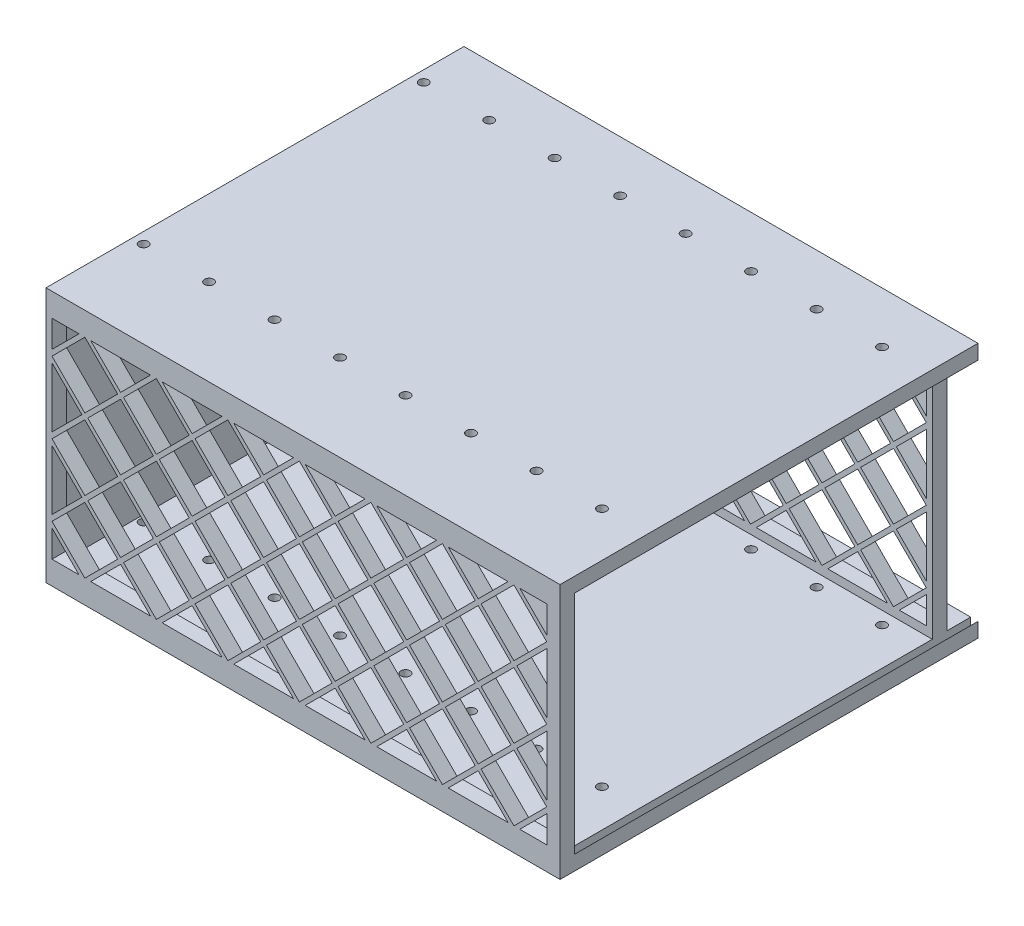
SolidWorks part; units mm, degrees
ref_plane "Front Plane" through (0, 0, 0) normal (0, 0, 1) x (1, 0, 0)
ref_plane "Top Plane" through (0, 0, 0) normal (0, 1, 0) x (1, 0, 0)
ref_plane "Right Plane" through (0, 0, 0) normal (1, 0, 0) x (0, 0, -1)
sketch "Sketch1" plane through (0, 0, 0) normal (0, 1, 0) x (1, 0, 0)
  line L1 (0, 0) -> (140.589, 0)
  line L2 (0, 0) -> (0, 114.3)
  line L3 (0, 114.3) -> (140.589, 114.3)
  line L4 (140.589, 0) -> (140.589, 114.3)
  dimension "D1" = 140.589
  dimension "D2" = 114.3
extrude "Boss-Extrude1" add sketch "Sketch1" along normal blind 69.85
sketch "Sketch4" plane through (140.589, 0, 0) normal (1, 0, 0) x (0, 0, -1)
  line L0 (114.3, 69.85) -> (114.3, 0) construction
  line L1 (114.3, 65.85) -> (107.8, 65.85)
  line L2 (114.3, 65.85) -> (114.3, 4)
  line L3 (114.3, 4) -> (107.8, 4)
  line L4 (107.8, 65.85) -> (107.8, 4)
  line L5 (107.8, 0) -> (107.8, 4) construction
  line L6 (0, 0) -> (114.3, 0) construction
  line L7 (107.8, 65.85) -> (107.8, 69.85) construction
  line L8 (0, 69.85) -> (114.3, 69.85) construction
  dimension "D1" = 6.5
  dimension "D2" = 4
extrude "Cut-Extrude2" cut sketch "Sketch4" against normal through all
sketch "Sketch3" plane through (140.589, 0, 0) normal (1, 0, 0) x (0, 0, -1)
  line L0 (4, 65.85) -> (0, 65.85) construction
  line L1 (4, 65.85) -> (103.8, 65.85)
  line L2 (4, 65.85) -> (4, 4)
  line L3 (4, 4) -> (103.8, 4)
  line L4 (103.8, 65.85) -> (103.8, 4)
  line L5 (0, 69.85) -> (0, 0) construction
  line L6 (103.8, 4) -> (107.8, 4) construction
  line L8 (103.8, 0) -> (103.8, 4) construction
  line L9 (0, 0) -> (114.3, 0) construction
  line L10 (4, 65.85) -> (4, 69.85) construction
  line L11 (0, 69.85) -> (114.3, 69.85) construction
  line L12 (107.8, 65.85) -> (107.8, 4) construction
  dimension "D1" = 4
extrude "Cut-Extrude3" cut sketch "Sketch3" against normal offset from surface (139.389 mm away) 1.2 up to face at (0, 34.925, -84.1)
sketch "Sketch2" plane through (0, 69.85, 0) normal (0, 1, 0) x (1, 0, 0)
  line L0 (0, 23.7) -> (140.589, 23.7) construction
  line L1 (0, 114.3) -> (0, 0) construction
  line L2 (140.589, 0) -> (140.589, 114.3) construction
  line L3 (0, 100.3) -> (140.589, 100.3) construction
  line L4 (25.527, 100.3) -> (25.527, 23.7) construction
  line L5 (140.589, 114.3) -> (0, 114.3) construction
  line L6 (43.434, 100.3) -> (43.434, 23.7) construction
  line L7 (61.341, 100.3) -> (61.341, 23.7) construction
  line L8 (79.248, 100.3) -> (79.248, 23.7) construction
  line L9 (97.155, 100.3) -> (97.155, 23.7) construction
  line L10 (115.062, 100.3) -> (115.062, 23.7) construction
  line L11 (132.969, 100.3) -> (132.969, 23.7) construction
  line L12 (7.62, 100.3) -> (7.62, 23.7) construction
  line L13 (7.62, 62) -> (25.527, 62) construction
  line L14 (25.527, 62) -> (43.434, 62) construction
  line L15 (43.434, 62) -> (61.341, 62) construction
  line L16 (61.341, 62) -> (79.248, 62) construction
  line L17 (79.248, 62) -> (97.155, 62) construction
  line L18 (97.155, 62) -> (115.062, 62) construction
  line L19 (115.062, 62) -> (132.969, 62) construction
  line L20 (7.62, 62) -> (0, 62) construction
  line L21 (132.969, 62) -> (140.589, 62) construction
  line L22 (3, 100.3) -> (3, 23.7) construction
  circle A0 centre (3, 100.3) radius 1.25
  circle A1 centre (3, 23.7) radius 1.25
  circle A2 centre (20.907, 100.3) radius 1.25
  circle A3 centre (20.907, 23.7) radius 1.25
  circle A4 centre (38.814, 100.3) radius 1.25
  circle A5 centre (38.814, 23.7) radius 1.25
  circle A6 centre (56.721, 100.3) radius 1.25
  circle A7 centre (56.721, 23.7) radius 1.25
  circle A8 centre (74.628, 100.3) radius 1.25
  circle A9 centre (74.628, 23.7) radius 1.25
  circle A10 centre (92.535, 100.3) radius 1.25
  circle A11 centre (92.535, 23.7) radius 1.25
  circle A12 centre (110.442, 100.3) radius 1.25
  circle A13 centre (110.442, 23.7) radius 1.25
  circle A14 centre (128.349, 100.3) radius 1.25
  circle A15 centre (128.349, 23.7) radius 1.25
  dimension "D4" = 3
  dimension "D5" = 2.5
  dimension "D1" = 14
  dimension "D2" = 90.6
  dimension "D3" = 17.907
  dimension "D7" = 17.907
  dimension "D6" = 8
extrude "Cut-Extrude1" cut sketch "Sketch2" against normal blind 4
ref_plane "Plane1" through (0, 34.925, 0) normal (0, 1, 0) x (1, 0, 0)
mirror "Mirror1" about plane through (0, 34.925, 0) normal (0, 1, 0) of "Cut-Extrude1"
sketch "Sketch5" plane through (0, 0, -114.3) normal (0, 0, -1) x (-1, 0, 0)
  line L0 (-138.589, 67.85) -> (-138.589, 2)
  line L1 (-138.589, 2) -> (-140.589, 4)
  line L2 (0, 4) -> (-140.589, 4) construction
  line L3 (-140.589, 4) -> (-140.589, 65.85)
  line L4 (0, 65.85) -> (-140.589, 65.85) construction
  line L5 (-140.589, 65.85) -> (-138.589, 67.85)
  line L6 (-138.589, 67.85) -> (-138.589, 69.85) construction
  line L7 (-140.589, 69.85) -> (0, 69.85) construction
  line L8 (-138.589, 2) -> (-138.589, 0) construction
  line L9 (-140.589, 0) -> (0, 0) construction
  line L10 (-140.589, 69.85) -> (-140.589, 65.85) construction
  dimension "D1" = 2
  dimension "D2" = 2
extrude "Cut-Extrude4" cut sketch "Sketch5" against normal up to surface (110.3 mm away) up to face at (70.8945, 34.925, -4)
sketch "Sketch6" plane through (0, 0, -107.8) normal (0, 0, -1) x (-1, 0, 0)
  line L0 (-136.9488, 54.483) -> (-127.9685, 45.5027)
  line L1 (-127.9685, 45.5027) -> (-118.9882, 54.483)
  line L2 (-118.9882, 54.483) -> (-127.9685, 63.4633)
  line L3 (-127.9685, 63.4633) -> (-136.9488, 54.483)
  line L4 (-108.4105, 63.4633) -> (-117.3908, 54.483)
  line L5 (-117.3908, 54.483) -> (-108.4105, 45.5027)
  line L6 (-108.4105, 45.5027) -> (-99.4302, 54.483)
  line L7 (-99.4302, 54.483) -> (-108.4105, 63.4633)
  line L8 (-88.8525, 63.4633) -> (-97.8328, 54.483)
  line L9 (-97.8328, 54.483) -> (-88.8525, 45.5027)
  line L10 (-88.8525, 45.5027) -> (-79.8722, 54.483)
  line L11 (-79.8722, 54.483) -> (-88.8525, 63.4633)
  line L12 (-69.2945, 63.4633) -> (-78.2748, 54.483)
  line L13 (-78.2748, 54.483) -> (-69.2945, 45.5027)
  line L14 (-69.2945, 45.5027) -> (-60.3142, 54.483)
  line L15 (-60.3142, 54.483) -> (-69.2945, 63.4633)
  line L16 (-49.7365, 63.4633) -> (-58.7168, 54.483)
  line L17 (-58.7168, 54.483) -> (-49.7365, 45.5027)
  line L18 (-49.7365, 45.5027) -> (-40.7562, 54.483)
  line L19 (-40.7562, 54.483) -> (-49.7365, 63.4633)
  line L20 (-30.1785, 63.4633) -> (-39.1588, 54.483)
  line L21 (-39.1588, 54.483) -> (-30.1785, 45.5027)
  line L22 (-30.1785, 45.5027) -> (-21.1982, 54.483)
  line L23 (-21.1982, 54.483) -> (-30.1785, 63.4633)
  line L24 (-10.6205, 63.4633) -> (-19.6008, 54.483)
  line L25 (-19.6008, 54.483) -> (-10.6205, 45.5027)
  line L26 (-10.6205, 45.5027) -> (-1.6402, 54.483)
  line L27 (-1.6402, 54.483) -> (-10.6205, 63.4633)
  line L28 (-108.4105, 43.9053) -> (-117.3908, 34.925)
  line L29 (-117.3908, 34.925) -> (-108.4105, 25.9447)
  line L30 (-108.4105, 25.9447) -> (-99.4302, 34.925)
  line L31 (-99.4302, 34.925) -> (-108.4105, 43.9053)
  line L32 (-88.8525, 43.9053) -> (-97.8328, 34.925)
  line L33 (-97.8328, 34.925) -> (-88.8525, 25.9447)
  line L34 (-88.8525, 25.9447) -> (-79.8722, 34.925)
  line L35 (-79.8722, 34.925) -> (-88.8525, 43.9053)
  line L36 (-69.2945, 43.9053) -> (-78.2748, 34.925)
  line L37 (-78.2748, 34.925) -> (-69.2945, 25.9447)
  line L38 (-69.2945, 25.9447) -> (-60.3142, 34.925)
  line L39 (-60.3142, 34.925) -> (-69.2945, 43.9053)
  line L40 (-49.7365, 43.9053) -> (-58.7168, 34.925)
  line L41 (-58.7168, 34.925) -> (-49.7365, 25.9447)
  line L42 (-49.7365, 25.9447) -> (-40.7562, 34.925)
  line L43 (-40.7562, 34.925) -> (-49.7365, 43.9053)
  line L44 (-30.1785, 43.9053) -> (-39.1588, 34.925)
  line L45 (-39.1588, 34.925) -> (-30.1785, 25.9447)
  line L46 (-30.1785, 25.9447) -> (-21.1982, 34.925)
  line L47 (-21.1982, 34.925) -> (-30.1785, 43.9053)
  line L48 (-10.6205, 43.9053) -> (-19.6008, 34.925)
  line L49 (-19.6008, 34.925) -> (-10.6205, 25.9447)
  line L50 (-10.6205, 25.9447) -> (-1.6402, 34.925)
  line L51 (-1.6402, 34.925) -> (-10.6205, 43.9053)
  line L52 (-108.4105, 24.3473) -> (-117.3908, 15.367)
  line L53 (-117.3908, 15.367) -> (-108.4105, 6.3867)
  line L54 (-108.4105, 6.3867) -> (-99.4302, 15.367)
  line L55 (-99.4302, 15.367) -> (-108.4105, 24.3473)
  line L56 (-88.8525, 24.3473) -> (-97.8328, 15.367)
  line L57 (-97.8328, 15.367) -> (-88.8525, 6.3867)
  line L58 (-88.8525, 6.3867) -> (-79.8722, 15.367)
  line L59 (-79.8722, 15.367) -> (-88.8525, 24.3473)
  line L60 (-69.2945, 24.3473) -> (-78.2748, 15.367)
  line L61 (-78.2748, 15.367) -> (-69.2945, 6.3867)
  line L62 (-69.2945, 6.3867) -> (-60.3142, 15.367)
  line L63 (-60.3142, 15.367) -> (-69.2945, 24.3473)
  line L64 (-49.7365, 24.3473) -> (-58.7168, 15.367)
  line L65 (-58.7168, 15.367) -> (-49.7365, 6.3867)
  line L66 (-49.7365, 6.3867) -> (-40.7562, 15.367)
  line L67 (-40.7562, 15.367) -> (-49.7365, 24.3473)
  line L68 (-30.1785, 24.3473) -> (-39.1588, 15.367)
  line L69 (-39.1588, 15.367) -> (-30.1785, 6.3867)
  line L70 (-30.1785, 6.3867) -> (-21.1982, 15.367)
  line L71 (-21.1982, 15.367) -> (-30.1785, 24.3473)
  line L72 (-10.6205, 24.3473) -> (-19.6008, 15.367)
  line L73 (-19.6008, 15.367) -> (-10.6205, 6.3867)
  line L74 (-10.6205, 6.3867) -> (-1.6402, 15.367)
  line L75 (-1.6402, 15.367) -> (-10.6205, 24.3473)
  line L76 (-127.9685, 43.9053) -> (-136.9488, 34.925)
  line L77 (-136.9488, 34.925) -> (-127.9685, 25.9447)
  line L78 (-127.9685, 25.9447) -> (-118.9882, 34.925)
  line L79 (-118.9882, 34.925) -> (-127.9685, 43.9053)
  line L80 (-127.9685, 24.3473) -> (-136.9488, 15.367)
  line L81 (-136.9488, 15.367) -> (-127.9685, 6.3867)
  line L82 (-127.9685, 6.3867) -> (-118.9882, 15.367)
  line L83 (-118.9882, 15.367) -> (-127.9685, 24.3473)
  line L84 (-127.9685, 63.4633) -> (-108.4105, 63.4633) construction
  line L85 (-127.9685, 63.4633) -> (-127.9685, 43.9053) construction
  line L86 (-136.9488, 54.483) -> (-138.589, 54.483) construction
  line L87 (-138.589, 65.85) -> (-138.589, 4) construction
  line L88 (0, 54.483) -> (-1.6402, 54.483) construction
  line L89 (0, 65.85) -> (0, 4) construction
  line L90 (-127.9685, 4) -> (-127.9685, 6.3867) construction
  line L91 (0, 4) -> (-138.589, 4) construction
  line L92 (-127.9685, 6.3867) -> (-127.9685, 65.85) construction
  line L93 (0, 65.85) -> (-138.589, 65.85) construction
  line L94 (-127.9685, 65.85) -> (-127.9685, 63.4633) construction
  line L95 (-127.1698, 44.704) -> (-118.1895, 35.7237)
  line L96 (-118.1895, 35.7237) -> (-109.2092, 44.704)
  line L97 (-109.2092, 44.704) -> (-118.1895, 53.6843)
  line L98 (-118.1895, 53.6843) -> (-127.1698, 44.704)
  line L99 (-122.6796, 49.1941) -> (-123.4784, 49.9929) construction
  line L100 (-113.6994, 49.1941) -> (-112.9006, 49.9929) construction
  line L101 (-107.6118, 44.704) -> (-98.6315, 35.7237)
  line L102 (-98.6315, 35.7237) -> (-89.6512, 44.704)
  line L103 (-89.6512, 44.704) -> (-98.6315, 53.6843)
  line L104 (-98.6315, 53.6843) -> (-107.6118, 44.704)
  line L105 (-88.0538, 44.704) -> (-79.0735, 35.7237)
  line L106 (-79.0735, 35.7237) -> (-70.0932, 44.704)
  line L107 (-70.0932, 44.704) -> (-79.0735, 53.6843)
  line L108 (-79.0735, 53.6843) -> (-88.0538, 44.704)
  line L109 (-68.4958, 44.704) -> (-59.5155, 35.7237)
  line L110 (-59.5155, 35.7237) -> (-50.5352, 44.704)
  line L111 (-50.5352, 44.704) -> (-59.5155, 53.6843)
  line L112 (-59.5155, 53.6843) -> (-68.4958, 44.704)
  line L113 (-48.9378, 44.704) -> (-39.9575, 35.7237)
  line L114 (-39.9575, 35.7237) -> (-30.9772, 44.704)
  line L115 (-30.9772, 44.704) -> (-39.9575, 53.6843)
  line L116 (-39.9575, 53.6843) -> (-48.9378, 44.704)
  line L117 (-29.3798, 44.704) -> (-20.3995, 35.7237)
  line L118 (-20.3995, 35.7237) -> (-11.4192, 44.704)
  line L119 (-11.4192, 44.704) -> (-20.3995, 53.6843)
  line L120 (-20.3995, 53.6843) -> (-29.3798, 44.704)
  line L121 (-107.6118, 25.146) -> (-98.6315, 16.1657)
  line L122 (-98.6315, 16.1657) -> (-89.6512, 25.146)
  line L123 (-89.6512, 25.146) -> (-98.6315, 34.1263)
  line L124 (-98.6315, 34.1263) -> (-107.6118, 25.146)
  line L125 (-88.0538, 25.146) -> (-79.0735, 16.1657)
  line L126 (-79.0735, 16.1657) -> (-70.0932, 25.146)
  line L127 (-70.0932, 25.146) -> (-79.0735, 34.1263)
  line L128 (-79.0735, 34.1263) -> (-88.0538, 25.146)
  line L129 (-68.4958, 25.146) -> (-59.5155, 16.1657)
  line L130 (-59.5155, 16.1657) -> (-50.5352, 25.146)
  line L131 (-50.5352, 25.146) -> (-59.5155, 34.1263)
  line L132 (-59.5155, 34.1263) -> (-68.4958, 25.146)
  line L133 (-48.9378, 25.146) -> (-39.9575, 16.1657)
  line L134 (-39.9575, 16.1657) -> (-30.9772, 25.146)
  line L135 (-30.9772, 25.146) -> (-39.9575, 34.1263)
  line L136 (-39.9575, 34.1263) -> (-48.9378, 25.146)
  line L137 (-29.3798, 25.146) -> (-20.3995, 16.1657)
  line L138 (-20.3995, 16.1657) -> (-11.4192, 25.146)
  line L139 (-11.4192, 25.146) -> (-20.3995, 34.1263)
  line L140 (-20.3995, 34.1263) -> (-29.3798, 25.146)
  line L141 (-127.1698, 25.146) -> (-118.1895, 16.1657)
  line L142 (-118.1895, 16.1657) -> (-109.2092, 25.146)
  line L143 (-109.2092, 25.146) -> (-118.1895, 34.1263)
  line L144 (-118.1895, 34.1263) -> (-127.1698, 25.146)
  line L145 (-127.1698, 44.704) -> (-107.6118, 44.704) construction
  line L146 (-127.1698, 44.704) -> (-127.1698, 25.146) construction
  line L147 (-136.9488, 52.8855) -> (-136.9488, 36.5225)
  line L148 (-136.9488, 36.5225) -> (-128.7672, 44.704)
  line L149 (-128.7672, 44.704) -> (-136.9488, 52.8855)
  line L150 (-128.7672, 44.704) -> (-127.9685, 45.5027) construction
  line L151 (-128.7672, 44.704) -> (-127.9685, 43.9053) construction
  line L152 (-128.7672, 25.146) -> (-136.9488, 33.3275)
  line L153 (-136.9488, 33.3275) -> (-136.9488, 16.9645)
  line L154 (-136.9488, 16.9645) -> (-128.7672, 25.146)
  line L155 (-128.7672, 44.704) -> (-128.7672, 25.146) construction
  line L156 (-69.2945, 65.85) -> (-69.2945, 4) construction
  line L157 (-136.9488, 56.0805) -> (-136.9488, 63.4633)
  line L158 (-136.9488, 63.4633) -> (-129.566, 63.4633)
  line L159 (-129.566, 63.4633) -> (-136.9488, 56.0805)
  line L160 (-132.4586, 58.9731) -> (-133.2574, 59.7719) construction
  line L161 (-127.9685, 63.4633) -> (-129.566, 63.4633) construction
  line L162 (-136.9488, 13.7695) -> (-136.9488, 6.3867)
  line L163 (-136.9488, 6.3867) -> (-129.566, 6.3867)
  line L164 (-129.566, 6.3867) -> (-136.9488, 13.7695)
  line L165 (-132.4586, 10.8769) -> (-133.2574, 10.0781) construction
  line L166 (-136.9488, 13.7695) -> (-136.9488, 15.367) construction
  line L167 (-129.566, 6.3867) -> (-127.9685, 6.3867) construction
  line L168 (-1.6402, 6.3867) -> (-9.023, 6.3867)
  line L169 (-1.6402, 13.7695) -> (-1.6402, 6.3867)
  line L170 (-9.023, 6.3867) -> (-1.6402, 13.7695)
  line L171 (-1.6402, 16.9645) -> (-9.8218, 25.146)
  line L172 (-1.6402, 33.3275) -> (-1.6402, 16.9645)
  line L173 (-9.8218, 25.146) -> (-1.6402, 33.3275)
  line L174 (-1.6402, 36.5225) -> (-9.8218, 44.704)
  line L175 (-1.6402, 52.8855) -> (-1.6402, 36.5225)
  line L176 (-9.8218, 44.704) -> (-1.6402, 52.8855)
  line L177 (-1.6402, 63.4633) -> (-9.023, 63.4633)
  line L178 (-1.6402, 56.0805) -> (-1.6402, 63.4633)
  line L179 (-9.023, 63.4633) -> (-1.6402, 56.0805)
  line L180 (-126.371, 6.3867) -> (-110.008, 6.3867)
  line L181 (-110.008, 6.3867) -> (-118.1895, 14.5683)
  line L182 (-118.1895, 14.5683) -> (-126.371, 6.3867)
  line L183 (-118.1895, 14.5683) -> (-117.3908, 15.367) construction
  line L184 (-118.9882, 15.367) -> (-118.1895, 14.5683) construction
  line L185 (-98.6315, 14.5683) -> (-106.813, 6.3867)
  line L186 (-106.813, 6.3867) -> (-90.45, 6.3867)
  line L187 (-90.45, 6.3867) -> (-98.6315, 14.5683)
  line L188 (-79.0735, 14.5683) -> (-87.255, 6.3867)
  line L189 (-87.255, 6.3867) -> (-70.892, 6.3867)
  line L190 (-70.892, 6.3867) -> (-79.0735, 14.5683)
  line L191 (-59.5155, 14.5683) -> (-67.697, 6.3867)
  line L192 (-67.697, 6.3867) -> (-51.334, 6.3867)
  line L193 (-51.334, 6.3867) -> (-59.5155, 14.5683)
  line L194 (-39.9575, 14.5683) -> (-48.139, 6.3867)
  line L195 (-48.139, 6.3867) -> (-31.776, 6.3867)
  line L196 (-31.776, 6.3867) -> (-39.9575, 14.5683)
  line L197 (-20.3995, 14.5683) -> (-28.581, 6.3867)
  line L198 (-28.581, 6.3867) -> (-12.218, 6.3867)
  line L199 (-12.218, 6.3867) -> (-20.3995, 14.5683)
  line L200 (-118.1895, 14.5683) -> (-98.6315, 14.5683) construction
  line L201 (-138.589, 34.925) -> (0, 34.925) construction
  line L202 (-12.218, 63.4633) -> (-20.3995, 55.2817)
  line L203 (-28.581, 63.4633) -> (-12.218, 63.4633)
  line L204 (-20.3995, 55.2817) -> (-28.581, 63.4633)
  line L205 (-31.776, 63.4633) -> (-39.9575, 55.2817)
  line L206 (-48.139, 63.4633) -> (-31.776, 63.4633)
  line L207 (-39.9575, 55.2817) -> (-48.139, 63.4633)
  line L208 (-51.334, 63.4633) -> (-59.5155, 55.2817)
  line L209 (-67.697, 63.4633) -> (-51.334, 63.4633)
  line L210 (-59.5155, 55.2817) -> (-67.697, 63.4633)
  line L211 (-70.892, 63.4633) -> (-79.0735, 55.2817)
  line L212 (-87.255, 63.4633) -> (-70.892, 63.4633)
  line L213 (-79.0735, 55.2817) -> (-87.255, 63.4633)
  line L214 (-90.45, 63.4633) -> (-98.6315, 55.2817)
  line L215 (-106.813, 63.4633) -> (-90.45, 63.4633)
  line L216 (-98.6315, 55.2817) -> (-106.813, 63.4633)
  line L217 (-110.008, 63.4633) -> (-118.1895, 55.2817)
  line L218 (-126.371, 63.4633) -> (-110.008, 63.4633)
  line L219 (-118.1895, 55.2817) -> (-126.371, 63.4633)
  dimension "D1" = 12.7
  dimension "D4" = 19.558
  dimension "D5" = 19.558
  dimension "D6" = 45
  dimension "D9" = 19.558
  dimension "D10" = 19.558
  dimension "D11" = 2
  dimension "D12" = 19.558
  dimension "D14" = 19.558
  dimension "D2" = 7
  dimension "D3" = 3
  dimension "D7" = 6
  dimension "D8" = 2
  dimension "D13" = 6
extrude "Cut-Extrude5" cut sketch "Sketch6" against normal blind 4
ref_plane "Plane2" through (0, 0, -53.9) normal (0, 0, 1) x (1, 0, 0)
mirror "Mirror2" about plane through (0, 0, -53.9) normal (0, 0, 1) of "Cut-Extrude5"
